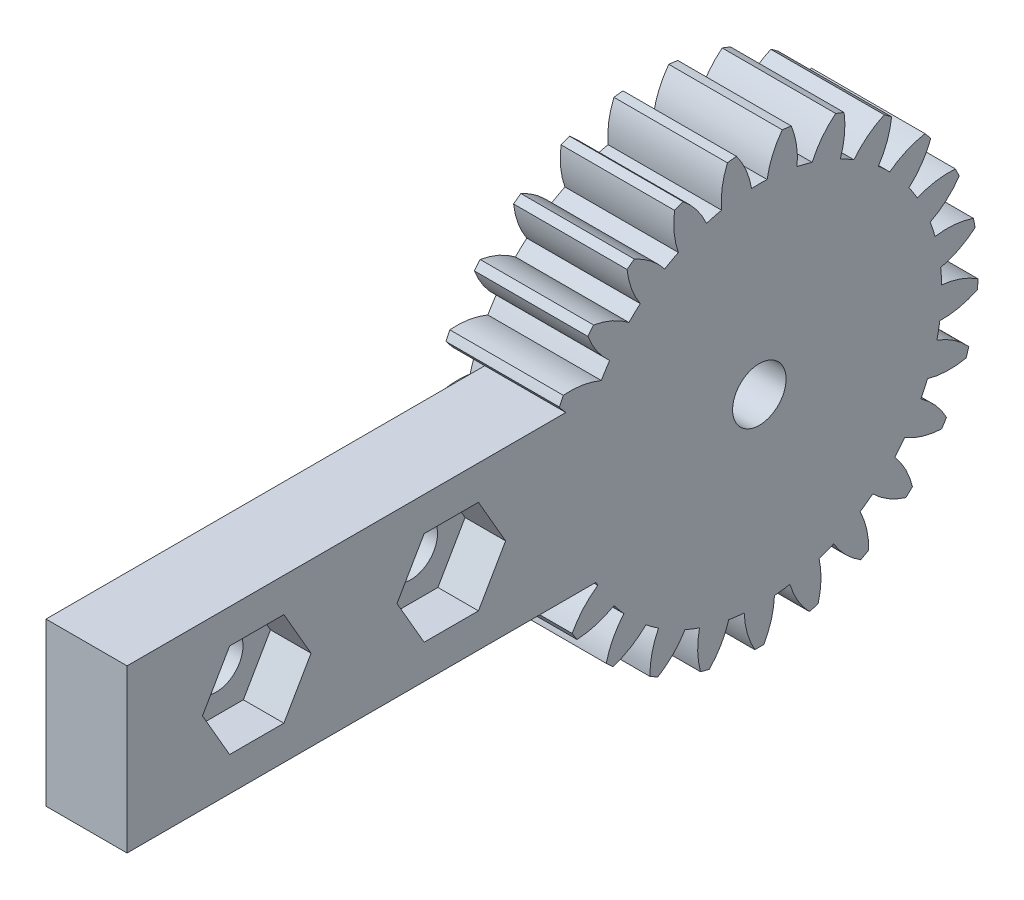
SolidWorks part; units mm, degrees
ref_plane "Plane1" through (0, 0, 0) normal (0, 0, 1) x (1, 0, 0)
ref_plane "Plane2" through (0, 0, 0) normal (0, 1, 0) x (1, 0, 0)
ref_plane "Plane3" through (0, 0, 0) normal (1, 0, 0) x (0, 0, -1)
sketch "HoldingSke" plane through (0, 0, 0) normal (0, 1, 0) x (1, 0, 0)
  line L0 (0, 0) -> (0.9063, -0.4226)
  line L1 (-15, 0) -> (100, 0) construction
  line L2 (0, 0) -> (-2.1039, 2.3779)
  line L3 (0, 0) -> (-11.863, 4.5341)
  line L4 (0, 0) -> (7.8269, 3.6497)
  line L5 (0, 0) -> (-46.8476, -17.4728)
  line L6 (0, 0) -> (-5.8027, -3.9151)
  line L7 (-2.1039, 2.3779) -> (8.6586, 51.2059)
  line L8 (-76.2, 54.61) -> (-76.1, 54.61)
  line L9 (-71.009, 38.7566) -> (-53.1078, 45.2721)
  line L10 (-76.2, 71.12) -> (104.1128, 71.12)
  line L11 (0, 0) -> (-7, 0)
  line L12 (-76.2, 101.6) -> (-76.162, 101.6)
  line L13 (24.9733, 27.94) -> (52.9518, 28.4284)
  line L14 (24.9733, 27.94) -> (24.9743, 27.94)
  line L15 (24.9733, 27.94) -> (100.4006, 29.5858)
  line L16 (-63.627, -1) -> (-12.827, -1)
  circle A0 centre (0, 0) radius 0.4
  circle A1 centre (0, 0) radius 11.249
  circle A2 centre (0, 0) radius 37.5
  circle A3 centre (0, 0) radius 0.4
  dimension "MHD" = 22.498
  dimension "Hub_dia" = 75
  dimension "Bore" = 0.8
  dimension "MBD" = 0.8
  dimension "Num_teeth" = 25
  dimension "Pitch" = 1
  dimension "Overall_len" = 50
  dimension "Show_teeth" = 25
  dimension "Thickness" = 7
  dimension "OAL" = 50.0001
  dimension "T_dim" = 0.1
  dimension "Ap" = 20
  dimension "H" = 19.05
  dimension "Pitch_radius" = 180.3128
  dimension "Width" = 7
  dimension "Backlash" = 0.038
  dimension "Addendum_fac" = 1
  dimension "Dedendum_fac" = 1.25
  dimension "Clearance_fac" = 0.25
  dimension "Dedendum_add" = 0.001
  dimension "Module" = 1
sketch "BasProSke" plane through (0, 0, 0) normal (0, 1, 0) x (1, 0, 0)
  line L0 (-10, 0) -> (60, 0) construction
  line L1 (0, 0) -> (0, 13.5)
  line L2 (0, 0) -> (7, 0)
  line L3 (7, 0) -> (7, 13.5)
  line L4 (7, 13.5) -> (0, 13.5)
  dimension "Thickness" = 7
  dimension "Diameter" = 27
revolve "Base-Revolve" add sketch "BasProSke" angle 360 about L0
sketch "TooCutSke" plane through (0, 0, 0) normal (1, 0, 0) x (0, 0, -1)
  line L1 (0, 0) -> (0, 107) construction
  line L2 (0, 0) -> (-0.8514, 12.471) construction
  line L3 (0, 0) -> (-3.1282, 24.7619) construction
  line L4 (-0.8514, 12.471) -> (-1.5641, 12.3809) construction
  arc A0 (0.4801, 11.2388) -> (-0.4801, 11.2388) centre (0, 0) ccw
  arc A1 (1.4322, 13.4494) -> (-1.4322, 13.4494) centre (0, 0) ccw
  circle A2 centre (0, 0) radius 12.5 construction
  circle A3 centre (0, 0) radius 11.7462 construction
  arc A4 (-0.4801, 11.2388) -> (-1.4322, 13.4494) centre (-5.4133, 10.4244) ccw
  arc A5 (1.4322, 13.4494) -> (0.4801, 11.2388) centre (5.4133, 10.4244) ccw
  dimension "Root_dia" = 22.498
  dimension "Overcut_dia" = 27.0508
  dimension "Pitch_dia" = 25
  dimension "Base_dia" = 23.4923
  dimension "Flank_rad" = 5
  dimension "Half_ang" = 7.2
  dimension "Half_CT" = 0.7184
extrude "ToothCut" cut sketch "TooCutSke" along normal through all
fillet "Breaks" [suppressed] radius 0.02
fillet "RootFillets" [suppressed] radius 0.251
pattern_circular "TeethCuts" count 25 every 14.4 about axis through (-10, 0, 0) along (1, 0, 0) of "ToothCut", "RootFillets", "Breaks"
sketch "HubNeaOneSke" plane through (0, 0, 0) normal (-1, 0, 0) x (0, 0, 1)
  circle A0 centre (0, 0) radius 11.249
  dimension "Diameter" = 22.498
extrude "HubNearOne" [suppressed] add sketch "HubNeaOneSke" along normal blind 43.0001
sketch "HubNeaBotSke" plane through (0, 0, 0) normal (-1, 0, 0) x (0, 0, 1)
  circle A0 centre (0, 0) radius 11.249
  dimension "Diameter" = 22.498
extrude "HubNearBoth" [suppressed] add sketch "HubNeaBotSke" along normal blind 21.5
ref_plane "FarPln" through (7, 0, 0) normal (1, 0, 0) x (0, 0, -1)
sketch "HubFarSke" plane through (7, 0, 0) normal (1, 0, 0) x (0, 0, -1)
  circle A0 centre (0, 0) radius 11.249
  dimension "Diameter" = 22.498
extrude "HubFar" [suppressed] add sketch "HubFarSke" along normal blind 21.5
sketch "BorSke" plane through (0, 0, 0) normal (1, 0, 0) x (0, 0, -1)
  circle A0 centre (0, 0) radius 0.4
  dimension "Diameter" = 0.8
extrude "Bore" cut sketch "BorSke" along normal mid plane 100.0001
sketch "KeySke" plane through (0, 0, 0) normal (1, 0, 0) x (0, 0, -1)
  line L0 (-0.05, 0) -> (-0.05, 0.5)
  line L1 (-0.05, 0.5) -> (0.05, 0.5)
  line L2 (0.05, 0.5) -> (0.05, 0)
  line L3 (0, 0) -> (0, 34) construction
  line L4 (-0.05, 0) -> (0.05, 0)
  dimension "Offset" = 0.5
  dimension "Width" = 0.1
extrude "Keyway" [suppressed] cut sketch "KeySke" along normal mid plane 100.0001
pattern_circular "Keyway2" [suppressed] count 2 every 90 about axis through (-10, 0, 0) along (1, 0, 0)
sketch "草图1" plane through (7, 0, 0) normal (1, 0, 0) x (0, 0, -1)
  circle A0 centre (0, 0) radius 1.65
  dimension "D1" = 3.3
extrude "切除-拉伸1" cut sketch "草图1" against normal blind 10
sketch "草图2" plane through (7, 0, 0) normal (1, 0, 0) x (0, 0, -1)
  line L1 (-9, 5) -> (-39, 5)
  line L2 (-9, 5) -> (-9, -5)
  line L3 (-9, -5) -> (-39, -5)
  line L4 (-39, 5) -> (-39, -5)
  circle A0 centre (0, 0) radius 1.65 construction
  circle A1 centre (-31, 0) radius 1.65
  circle A2 centre (-19, 0) radius 1.65
  dimension "D7" = 3.3
  dimension "D8" = 3.3
  dimension "D1" = 5
  dimension "D2" = 10
  dimension "D3" = 9
  dimension "D4" = 30
  dimension "D5" = 8
  dimension "D6" = 12
  dimension "D9" = 5
extrude "凸台-拉伸2" add sketch "草图2" against normal blind 5
sketch "草图3" plane through (7, 0, 0) normal (1, 0, 0) x (0, 0, -1)
  line L1 (-27.6514, 0) -> (-29.3257, 2.9)
  line L2 (-29.3257, 2.9) -> (-32.6743, 2.9)
  line L3 (-32.6743, 2.9) -> (-34.3486, 0)
  line L4 (-34.3486, 0) -> (-32.6743, -2.9)
  line L5 (-32.6743, -2.9) -> (-29.3257, -2.9)
  line L6 (-29.3257, -2.9) -> (-27.6514, 0)
  line L7 (-15.6514, 0) -> (-17.3257, 2.9)
  line L8 (-17.3257, 2.9) -> (-20.6743, 2.9)
  line L9 (-20.6743, 2.9) -> (-22.3486, 0)
  line L10 (-22.3486, 0) -> (-20.6743, -2.9)
  line L11 (-20.6743, -2.9) -> (-17.3257, -2.9)
  line L12 (-17.3257, -2.9) -> (-15.6514, 0)
  circle A0 centre (-31, 0) radius 2.9 construction
  circle A1 centre (-19, 0) radius 2.9 construction
  dimension "D1" = 5.8
  dimension "D2" = 5.8
extrude "切除-拉伸2" cut sketch "草图3" against normal blind 2.5
equation "' \"Module@HoldingSke\" = 6.35"
equation "' \"Num_teeth@HoldingSke\" = 12"
equation "' \"Ap@HoldingSke\" =  20"
equation "' \"Ap@HoldingSke\" = 20"
equation "' \"Width@HoldingSke\" = 0.5 * 25.4"
equation "' \"Hub_dia@HoldingSke\"= 1 * 25.4"
equation "' \"Hub_dia@HoldingSke\" = 1 * 25.4"
equation "' \"Overall_len@HoldingSke\" = 1.0 * 25.4"
equation "' \"Bore@HoldingSke\" = 0.75 * 25.4"
equation "' \"T_dim@HoldingSke\" = 0.1 * 25.4"
equation "' \"Width@KeySke\" = 0.25 * 25.4"
equation "' \"Show_teeth@HoldingSke\" = 13"
equation "' \"Backlash@HoldingSke\" = 0.009 * 25.4"
equation "' \"Addendum_fac@HoldingSke\" = 1.0"
equation "' \"Dedendum_fac@HoldingSke\" = 1.25"
equation "' \"Dedendum_add@HoldingSke\" = 0.00005 * 25.4"
equation "' \"Clearance_fac@HoldingSke\" = 0.25"
equation "\"Pitch@HoldingSke\" = 1 / \"Module@HoldingSke\""
equation "\"Overcut_dia@TooCutSke\" = (\"Num_teeth@HoldingSke\" + 2 * \"Addendum_fac@HoldingSke\") / \"Pitch@HoldingSke\" + 0.002 * 25.4"
equation "\"Pitch_dia@TooCutSke\" = \"Num_teeth@HoldingSke\" / \"Pitch@HoldingSke\""
equation "\"Base_dia@TooCutSke\" = \"Num_teeth@HoldingSke\" / \"Pitch@HoldingSke\" * cos((\"Ap@HoldingSke\"  * 3.14159265 / 180))"
equation "\"Root_dia@TooCutSke\" = (\"Num_teeth@HoldingSke\" + 2) / \"Pitch@HoldingSke\" - 2 * (\"Addendum_fac@HoldingSke\" + \"Dedendum_fac@HoldingSke\") / \"Pitch@HoldingSke\" - \"Dedendum_add@HoldingSke\" * 2"
equation "\"Half_ang@TooCutSke\" = 180 / \"Num_teeth@HoldingSke\""
equation "\"Half_CT@TooCutSke\" = \"Num_teeth@HoldingSke\" / \"Pitch@HoldingSke\" * sin((3.14159265 / 2 / \"Num_teeth@HoldingSke\")) / 2 - 7 * \"Backlash@HoldingSke\" / 4"
equation "\"Flank_rad@TooCutSke\" = \"Num_teeth@HoldingSke\" / \"Pitch@HoldingSke\" / 5"
equation "\"Radius@RootFillets\" = \"Clearance_fac@HoldingSke\" / \"Pitch@HoldingSke\" + \"Dedendum_add@HoldingSke\""
equation "\"Break_rad@Breaks\" = 0.02 / \"Pitch@HoldingSke\""
equation "\"Thickness@HoldingSke\" = \"Width@HoldingSke\""
equation "\"OAL@HoldingSke\" = \"Thickness@HoldingSke\""
equation "\"MHD@HoldingSke\" = (\"Num_teeth@HoldingSke\" + 2) / \"Pitch@HoldingSke\" - 2 * (\"Addendum_fac@HoldingSke\" + \"Dedendum_fac@HoldingSke\")  / \"Pitch@HoldingSke\" - \"Dedendum_add@HoldingSke\" * 2"
equation "\"MBD@HoldingSke\" = (\"Num_teeth@HoldingSke\" + 2) / \"Pitch@HoldingSke\" - 2 * (\"Addendum_fac@HoldingSke\" + \"Dedendum_fac@HoldingSke\")  / \"Pitch@HoldingSke\" - \"Dedendum_add@HoldingSke\" * 2 - 0.002 * 25.4"
equation "\"MHD@HoldingSke\" = ((sgn( \"MHD@HoldingSke\" - \"Hub_dia@HoldingSke\" )-1)*( \"MHD@HoldingSke\" - \"Hub_dia@HoldingSke\" ))/-2+ \"Hub_dia@HoldingSke\""
equation "\"MBD@HoldingSke\" = ((sgn( \"MBD@HoldingSke\" - \"Bore@HoldingSke\" )-1)*( \"MBD@HoldingSke\" - \"Bore@HoldingSke\" ))/-2+ \"Bore@HoldingSke\""
equation "\"OAL@HoldingSke\" = ((sgn( \"OAL@HoldingSke\" - \"Overall_len@HoldingSke\" )+1)*( \"OAL@HoldingSke\" - \"Overall_len@HoldingSke\" ))/2 + \"Overall_len@HoldingSke\" + 0.000002 * 25.4"
equation "\"Num_teeth@TeethCuts\" = int( \"Show_teeth@HoldingSke\" ) + 1"
equation "\"Num_teeth@TeethCuts\" = ((sgn( \"Num_teeth@TeethCuts\" - \"Num_teeth@HoldingSke\" )-1)*( \"Num_teeth@TeethCuts\" - \"Num_teeth@HoldingSke\" ))/-2+ \"Num_teeth@HoldingSke\""
equation "\"Num_teeth@TeethCuts\" = ((sgn( \"Num_teeth@TeethCuts\" - 2.0)+1)*( \"Num_teeth@TeethCuts\" - 2.0))/2 +2.0"
equation "\"Angle@TeethCuts\" = 360.0 / \"Num_teeth@HoldingSke\""
equation "\"Diameter@BasProSke\" = (\"Num_teeth@HoldingSke\" + 2 * \"Addendum_fac@HoldingSke\") / \"Pitch@HoldingSke\""
equation "\"Thickness@BasProSke\"  = \"Thickness@HoldingSke\""
equation "' \"Fillet_rad@BasProSke\" =  \"Thickness@HoldingSke\" * 0.05"
equation "' \"Fillet_rad@BasProSke\" = \"Thickness@HoldingSke\" * 0.05"
equation "\"MHD@HoldingSke\" = ((sgn( \"MHD@HoldingSke\" - \"Root_dia@TooCutSke\" )-1)*( \"MHD@HoldingSke\" - \"Root_dia@TooCutSke\" ))/-2+ \"Root_dia@TooCutSke\""
equation "\"Diameter@HubNeaOneSke\" = \"MHD@HoldingSke\""
equation "\"Length@HubNearOne\" = \"OAL@HoldingSke\" - \"Thickness@BasProSke\""
equation "\"Diameter@HubNeaBotSke\" = \"MHD@HoldingSke\""
equation "\"Length@HubNearBoth\" = ( \"OAL@HoldingSke\" - \"Thickness@BasProSke\" ) / 2.0"
equation "\"Thickness@FarPln\" = \"Thickness@BasProSke\""
equation "\"Diameter@HubFarSke\" = \"MHD@HoldingSke\""
equation "\"Length@HubFar\" = ( \"OAL@HoldingSke\" - \"Thickness@BasProSke\" ) / 2.0"
equation "\"Diameter@BorSke\" = \"MBD@HoldingSke\""
equation "\"D1@Bore\" = \"OAL@HoldingSke\" * 2.0"
equation "\"D1@Keyway\" = \"OAL@HoldingSke\" * 2.0"
equation "\"Offset@KeySke\" = \"T_dim@HoldingSke\" + \"MBD@HoldingSke\" / 2.0"
